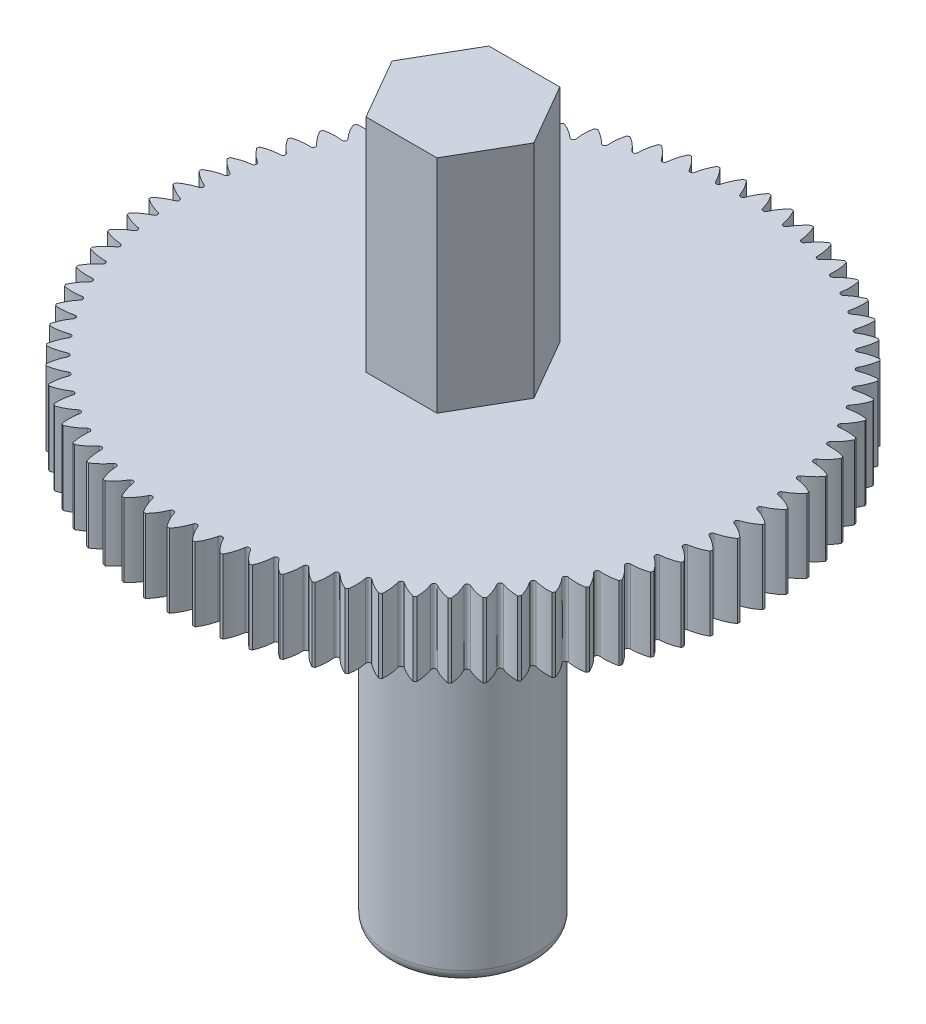
SolidWorks part; units mm, degrees
ref_plane "Front Plane" through (0, 0, 0) normal (0, 0, 1) x (1, 0, 0)
ref_plane "Top Plane" through (0, 0, 0) normal (0, 1, 0) x (1, 0, 0)
ref_plane "Right Plane" through (0, 0, 0) normal (1, 0, 0) x (0, 0, -1)
sketch "Sketch2" plane through (0, 0, 0) normal (0, 0, 1) x (1, 0, 0)
  line L0 (0, 0) -> (0, 29)
  line L1 (0, 0) -> (3, 0)
  line L2 (3, 0) -> (3, 17)
  line L3 (3, 17) -> (12, 17)
  line L4 (12, 17) -> (12, 20)
  line L5 (12, 20) -> (3, 20)
  line L6 (3, 20) -> (3, 29)
  line L7 (3, 29) -> (0, 29)
  dimension "D1" = 29
  dimension "D2" = 3
  dimension "D3" = 17
  dimension "D4" = 9
  dimension "D5" = 3
  dimension "D6" = 9
revolve "Revolve1" add sketch "Sketch2" angle 360 about L0
fillet "Fillet1" radius 0.5 1 edges at (0, 0, -3)
sketch "Sketch3" plane through (0, 29, 0) normal (0, 1, 0) x (1, 0, 0)
  line L1 (1.4434, 2.5) -> (-1.4434, 2.5)
  line L2 (-1.4434, 2.5) -> (-2.8868, 0)
  line L3 (-2.8868, 0) -> (-1.4434, -2.5)
  line L4 (-1.4434, -2.5) -> (1.4434, -2.5)
  line L5 (1.4434, -2.5) -> (2.8868, 0)
  line L6 (2.8868, 0) -> (1.4434, 2.5)
  circle A0 centre (0, 0) radius 2.5 construction
  circle A1 centre (0, 0) radius 3 construction
  circle A2 centre (0, 0) radius 3
  dimension "D1" = 5
extrude "Cut-Extrude1" cut sketch "Sketch3" against normal blind 9
sketch "Sketch4" plane through (0, 20, 0) normal (0, 1, 0) x (1, 0, 0)
  line L0 (0, 0) -> (0, 15.7858) construction
  arc A0 (-0.45, 11.9916) -> (-0.0942, 11.3714) centre (-1.979, 10.7023) cw
  circle A1 centre (0, 0) radius 12 construction
  arc A2 (0.45, 11.9916) -> (0.0942, 11.3714) centre (1.979, 10.7023) ccw
  arc A3 (0.45, 11.9916) -> (-0.45, 11.9916) centre (0, 0) ccw
  arc A4 (-0.0942, 11.3714) -> (0.0942, 11.3714) centre (0, 11.4049) ccw
  point P13 (0, 10.9916)
  dimension "D3" = 2
  dimension "D4" = 2
  dimension "D5" = 0.1
  dimension "D1" = 0.9
  dimension "D2" = 1
extrude "Cut-Extrude2" cut sketch "Sketch4" against normal up to next (3 mm away)
pattern_circular "CirPattern1" count 75 over 360 about axis through (0, 0, 0) along (0, 1, 0) of "Cut-Extrude2"
